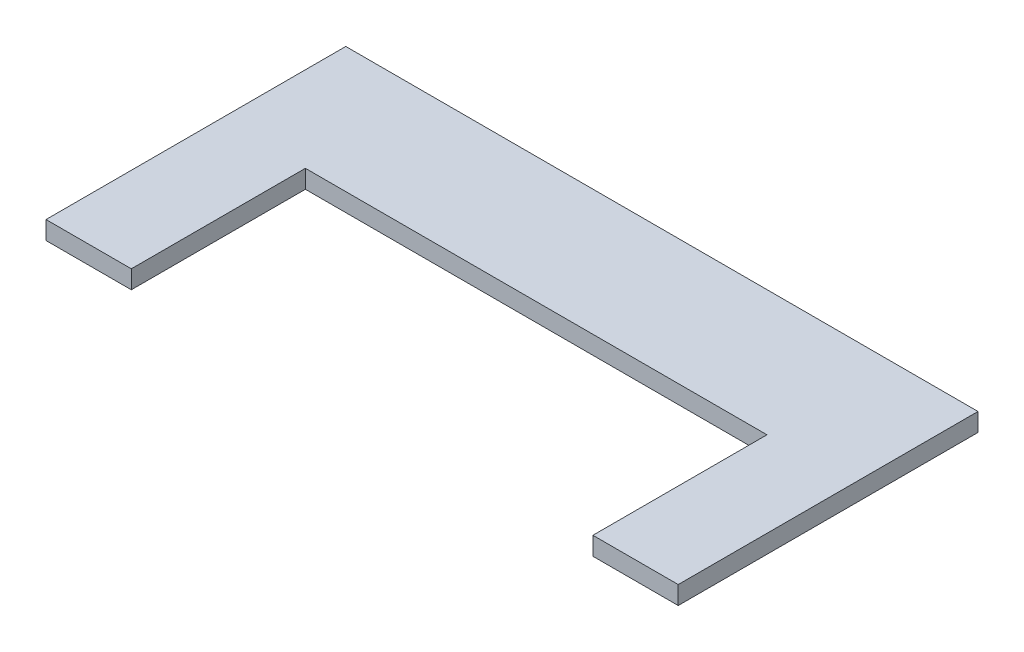
SolidWorks part; units mm, degrees
ref_plane "Front Plane" through (0, 0, 0) normal (0, 0, 1) x (1, 0, 0)
ref_plane "Top Plane" through (0, 0, 0) normal (0, 1, 0) x (1, 0, 0)
ref_plane "Right Plane" through (0, 0, 0) normal (1, 0, 0) x (0, 0, -1)
sketch "Sketch1" plane through (0, 0, 0) normal (0, 1, 0) x (1, 0, 0)
  line L0 (0, 0) -> (0, 52.7) construction
  line L1 (-55.5722, 52.7) -> (55.5722, 52.7)
  line L2 (-55.5722, 52.7) -> (-55.5722, 0)
  line L3 (-55.5722, 0) -> (55.5722, 0) construction
  line L4 (55.5722, 52.7) -> (55.5722, 0)
  line L6 (40.5722, 0) -> (40.5722, 30.6)
  line L7 (40.5722, 30.6) -> (-40.5722, 30.6)
  line L8 (-40.5722, 30.6) -> (-40.5722, 0)
  line L9 (55.5722, 0) -> (40.5722, 0)
  line L10 (-40.5722, 0) -> (-55.5722, 0)
  dimension "D1" = 15
sketch "Sketch2" plane through (0, 0, 0) normal (1, 0, 0) x (0, 0, -1)
  line L1 (0, 0) -> (52.7, 0)
  line L2 (0, 0) -> (0, 3.2)
  line L3 (0, 3.2) -> (52.7, 3.2)
  line L4 (52.7, 0) -> (52.7, 3.2)
  dimension "D1" = 3.2
extrude "Boss-Extrude1" add sketch "Sketch1" along normal up to vertex (3.2 mm away) up to point (0, 3.2, -52.7)
